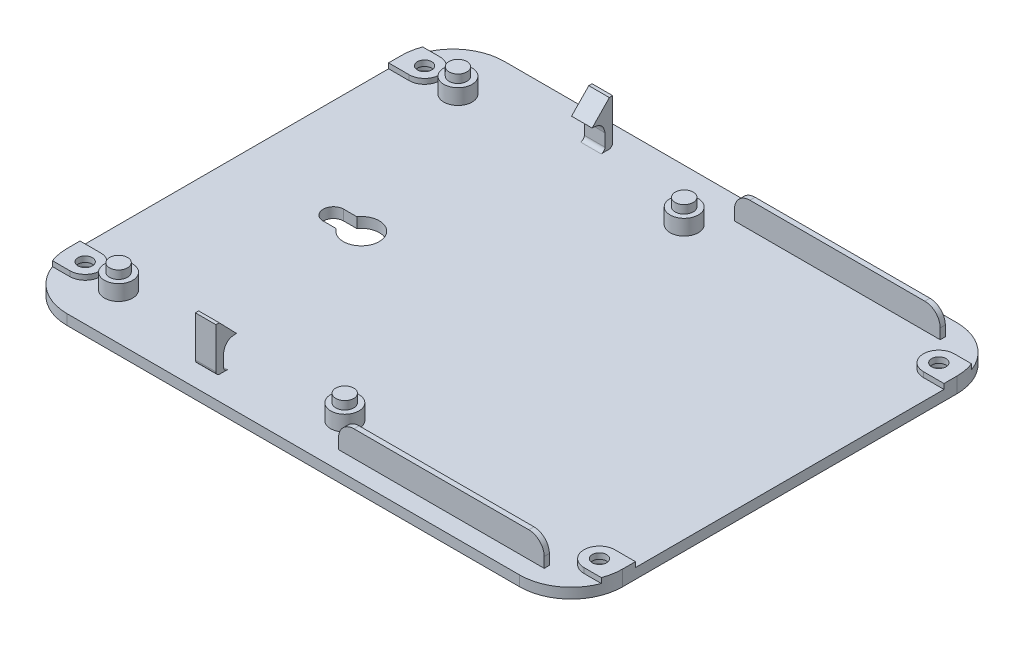
SolidWorks part; units mm, degrees
ref_plane "Front Plane" through (0, 0, 0) normal (0, 0, 1) x (1, 0, 0)
ref_plane "Top Plane" through (0, 0, 0) normal (0, 1, 0) x (1, 0, 0)
ref_plane "Right Plane" through (0, 0, 0) normal (1, 0, 0) x (0, 0, -1)
sketch "Sketch1" plane through (0, 0, 0) normal (0, 1, 0) x (1, 0, 0)
  line L0 (58.999, 8.4848) -> (96.6216, 8.4848) construction
  line L10 (-30.001, 50.9848) -> (57.999, 50.9848)
  line L11 (-40.001, 40.9848) -> (-40.001, -24.0152)
  line L12 (-30.001, -34.0152) -> (57.999, -34.0152)
  line L13 (67.999, 40.9848) -> (67.999, -24.0152)
  line L18 (-28.001, 48.9848) -> (55.999, 48.9848)
  line L19 (-38.001, 38.9848) -> (-38.001, -22.0152)
  line L20 (-28.001, -32.0152) -> (55.999, -32.0152)
  line L21 (65.999, 38.9848) -> (65.999, -22.0152)
  arc A12 (-40.001, 40.9848) -> (-30.001, 50.9848) centre (-30.001, 40.9848) cw
  arc A13 (-28.001, 48.9848) -> (-38.001, 38.9848) centre (-28.001, 38.9848) ccw
  arc A14 (67.999, -24.0152) -> (57.999, -34.0152) centre (57.999, -24.0152) cw
  arc A15 (65.999, -22.0152) -> (55.999, -32.0152) centre (55.999, -22.0152) cw
  arc A16 (67.999, 40.9848) -> (57.999, 50.9848) centre (57.999, 40.9848) ccw
  arc A17 (65.999, 38.9848) -> (55.999, 48.9848) centre (55.999, 38.9848) ccw
  arc A18 (-40.001, -24.0152) -> (-30.001, -34.0152) centre (-30.001, -24.0152) ccw
  arc A19 (-38.001, -22.0152) -> (-28.001, -32.0152) centre (-28.001, -22.0152) ccw
  point P0 (0, 0)
  point P6 (0, 0)
  point P29 (-28.001, 45.2348)
  point P31 (-28.001, 45.2348)
  point P35 (15.999, 45.2348)
  point P41 (15.999, -28.2652)
  point P47 (-28.001, -28.2652)
  dimension "D21" = 10
  dimension "D22" = 10
  dimension "D8" = 42.5
  dimension "D9" = 42.5
  dimension "D16" = 2
  dimension "D17" = 2
  dimension "D18" = 2
  dimension "D19" = 2
sketch "Sketch3" plane through (0, 0, 0) normal (0, 1, 0) x (1, 0, 0)
  line L0 (-30.001, -34.0152) -> (57.999, -34.0152) construction
  line L1 (67.999, 40.9848) -> (67.999, -24.0152) construction
  line L2 (-30.001, 50.9848) -> (57.999, 50.9848) construction
  line L3 (-40.001, 40.9848) -> (-40.001, -24.0152) construction
  line L4 (-30.001, -34.0152) -> (57.999, -34.0152)
  line L5 (67.999, 40.9848) -> (67.999, -24.0152)
  line L6 (-30.001, 50.9848) -> (57.999, 50.9848)
  line L7 (-40.001, 40.9848) -> (-40.001, -24.0152)
  arc A0 (-40.001, -24.0152) -> (-30.001, -34.0152) centre (-30.001, -24.0152) ccw construction
  arc A1 (57.999, -34.0152) -> (67.999, -24.0152) centre (57.999, -24.0152) ccw construction
  arc A2 (67.999, 40.9848) -> (57.999, 50.9848) centre (57.999, 40.9848) ccw construction
  arc A3 (-30.001, 50.9848) -> (-40.001, 40.9848) centre (-30.001, 40.9848) ccw construction
  arc A4 (-40.001, -24.0152) -> (-30.001, -34.0152) centre (-30.001, -24.0152) ccw
  arc A5 (57.999, -34.0152) -> (67.999, -24.0152) centre (57.999, -24.0152) ccw
  arc A6 (67.999, 40.9848) -> (57.999, 50.9848) centre (57.999, 40.9848) ccw
  arc A7 (-30.001, 50.9848) -> (-40.001, 40.9848) centre (-30.001, 40.9848) ccw
  dimension "D1" = 88
  dimension "D2" = 65
extrude "Boss-Extrude2" add sketch "Sketch3" along normal blind 2
sketch "Sketch5" plane through (0, 0, 34.0152) normal (0, 1, 0) x (1, 0, 0)
  line L0 (13.999, 83) -> (13.999, 110.4401) construction
  line L1 (-36.001, 78.5) -> (-39.3685, 78.5)
  line L2 (-36.001, 72.5) -> (-40.001, 72.5)
  line L3 (-40.001, 75) -> (-40.001, 10) construction
  line L4 (63.999, 78.5) -> (67.3665, 78.5)
  line L5 (63.999, 72.5) -> (67.999, 72.5)
  line L8 (63.999, 12.5) -> (67.999, 12.5)
  line L9 (67.999, 10) -> (67.999, 75) construction
  line L10 (63.999, 6.5) -> (67.3665, 6.5)
  line L11 (-36.001, 12.5) -> (-40.001, 12.5)
  line L12 (-36.001, 6.5) -> (-39.3685, 6.5)
  line L13 (67.999, 10) -> (67.999, 12.5)
  line L14 (-40.001, 75) -> (-40.001, 72.5)
  line L15 (67.999, 72.5) -> (67.999, 75)
  line L16 (-40.001, 12.5) -> (-40.001, 10)
  arc A0 (-30.001, 85) -> (-40.001, 75) centre (-30.001, 75) ccw construction
  arc A1 (67.999, 75) -> (57.999, 85) centre (57.999, 75) ccw construction
  arc A2 (57.999, 0) -> (67.999, 10) centre (57.999, 10) ccw construction
  arc A4 (-36.001, 6.5) -> (-36.001, 12.5) centre (-36.001, 9.5) ccw
  arc A5 (63.999, 12.5) -> (63.999, 6.5) centre (63.999, 9.5) ccw
  arc A6 (63.999, 78.5) -> (63.999, 72.5) centre (63.999, 75.5) ccw
  arc A7 (-36.001, 72.5) -> (-36.001, 78.5) centre (-36.001, 75.5) ccw
  arc A9 (-40.001, 10) -> (-30.001, 0) centre (-30.001, 10) ccw construction
  arc A10 (67.999, 75) -> (67.3665, 78.5) centre (57.999, 75) ccw
  arc A11 (67.3665, 6.5) -> (67.999, 10) centre (57.999, 10) ccw
  arc A12 (-40.001, 10) -> (-39.3685, 6.5) centre (-30.001, 10) ccw
  arc A13 (-39.3685, 78.5) -> (-40.001, 75) centre (-30.001, 75) ccw
  dimension "D1" = 6
  dimension "D2" = 6
  dimension "D3" = 6
  dimension "D4" = 6
  dimension "D5" = 50
  dimension "D6" = 50
  dimension "D7" = 50
  dimension "D8" = 50
sketch "Sketch6" plane through (0, 2, 0) normal (0, 1, 0) x (1, 0, 0)
  line L0 (-40.001, 8.4848) -> (67.999, 8.4848) construction
  line L1 (-40.001, 40.9848) -> (-40.001, -24.0152) construction
  line L2 (67.999, -24.0152) -> (67.999, 40.9848) construction
  line L3 (-15.3091, 50.9848) -> (-15.3091, -34.0152) construction
  line L4 (57.999, 50.9848) -> (-30.001, 50.9848) construction
  line L5 (-30.001, -34.0152) -> (57.999, -34.0152) construction
  line L6 (-16.9035, 8.4848) -> (-16.9035, 10.4848) construction
  line L8 (-16.9035, 8.4848) -> (-16.9035, 6.4848) construction
  line L9 (-16.9035, 8.4848) -> (-20.7218, 8.4848) construction
  line L10 (-18.1821, 6.4858) -> (-20.7218, 6.4858)
  line L11 (-18.1821, 10.4838) -> (-20.7218, 10.4838)
  arc A0 (-18.1821, 6.4858) -> (-18.1821, 10.4838) centre (-15.3091, 8.4848) ccw
  arc A2 (-20.7218, 10.4838) -> (-20.7218, 6.4858) centre (-20.7218, 8.4848) ccw
  point P16 (-18.8126, 8.4848)
  dimension "D1" = 7
  dimension "D2" = 2
  dimension "D3" = 2
  dimension "D4" = 1.5944
extrude "Cut-Extrude2" cut sketch "Sketch6" against normal blind 7 contours L11 A2 L10 A0
sketch "Sketch10" plane through (0, 0, 0) normal (0, 1, 0) x (1, 0, 0)
  line L0 (19.2632, 46.4848) -> (59.2632, 46.4848)
  line L1 (59.2632, 46.4848) -> (59.2632, 47.4848)
  line L2 (59.2632, 47.4848) -> (19.2632, 47.4848)
  line L3 (19.2632, 47.4848) -> (19.2632, 46.4848)
  line L4 (19.2632, -29.5152) -> (59.2632, -29.5152)
  line L5 (59.2632, -29.5152) -> (59.2632, -30.5152)
  line L6 (59.2632, -30.5152) -> (19.2632, -30.5152)
  line L7 (19.2632, -30.5152) -> (19.2632, -29.5152)
  line L8 (60.2632, 8.4848) -> (81.8858, 8.4848) construction
  dimension "D1" = 1
  dimension "D2" = 1
  dimension "D3" = 38
  dimension "D4" = 38
extrude "Boss-Extrude3" add sketch "Sketch10" along normal blind 7
sketch "Sketch12" plane through (0, 0, 30.5152) normal (0, 0, 1) x (1, 0, 0)
  line L0 (56.2632, 7) -> (59.2632, 7)
  line L1 (59.2632, 7) -> (59.2632, 2) construction
  line L2 (19.2632, 7) -> (59.2632, 7) construction
  line L3 (59.2632, 7) -> (59.2632, 4)
  line L4 (19.2632, 4) -> (19.2632, 7)
  line L5 (19.2632, 7) -> (19.2632, 2) construction
  line L6 (19.2632, 7) -> (22.2632, 7)
  arc A0 (59.2632, 4) -> (56.2632, 7) centre (56.2632, 4) ccw
  arc A1 (19.2632, 4) -> (22.2632, 7) centre (22.2632, 4) cw
  dimension "D2" = 3
extrude "Cut-Extrude4" cut sketch "Sketch12" against normal up to surface (1 mm away) up to face at (39.2632, 4.5, 29.5152)
sketch "Sketch13" plane through (0, 0, -47.4848) normal (0, 0, -1) x (-1, 0, 0)
  line L0 (-56.2632, 7) -> (-59.2632, 7)
  line L1 (-59.2632, 7) -> (-19.2632, 7) construction
  line L2 (-59.2632, 7) -> (-59.2632, 4)
  line L3 (-19.2632, 4) -> (-19.2632, 7)
  line L4 (-19.2632, 7) -> (-19.2632, 2) construction
  line L5 (-19.2632, 7) -> (-22.2632, 7)
  arc A0 (-19.2632, 4) -> (-22.2632, 7) centre (-22.2632, 4) ccw construction
  arc A1 (-56.2632, 7) -> (-59.2632, 4) centre (-56.2632, 4) ccw construction
  arc A2 (-19.2632, 4) -> (-22.2632, 7) centre (-22.2632, 4) ccw
  arc A3 (-56.2632, 7) -> (-59.2632, 4) centre (-56.2632, 4) ccw
extrude "Cut-Extrude5" cut sketch "Sketch13" against normal up to surface (1 mm away) up to face at (39.2632, 4.5, -46.4848)
sketch "Sketch14" plane through (0, 0, 0) normal (0, -1, 0) x (1, 0, 0)
  circle A0 centre (-29.011, 25.0118) radius 1.75
  circle A1 centre (14.9819, 25.0118) radius 1.75
  circle A2 centre (14.9819, -40.9882) radius 1.75
  circle A3 centre (-29.011, -40.9882) radius 1.75
  dimension "D1" = 3.5
extrude "Boss-Extrude4" add sketch "Sketch14" against normal up to surface (6.6 mm away) contours A0 | A1 | A2 | A3
sketch "Sketch15" plane through (0, 0, 0) normal (0, -1, 0) x (1, 0, 0)
  circle A0 centre (-29.011, 25.0118) radius 2.75
  circle A1 centre (14.9819, 25.0118) radius 2.75
  circle A2 centre (14.9819, -40.9882) radius 2.75
  circle A3 centre (-29.011, -40.9882) radius 2.75
  dimension "D1" = 5.5
extrude "Boss-Extrude5" add sketch "Sketch15" against normal up to surface (5 mm away)
ref_plane "Plane1" through (-7, 0, 0) normal (1, 0, 0) x (0, 0, -1)
sketch "Sketch19" plane through (-7, 0, 0) normal (1, 0, 0) x (0, 0, -1)
  line L4 (-30.0919, 10.6908) -> (-30.0919, 2.75)
  line L5 (-29.8901, 0) -> (-28.5919, 0)
  line L6 (-28.5919, 2.75) -> (-28.5919, 5.1849)
  line L7 (-26.0931, 7.2293) -> (-29.4468, 10.6908)
  line L8 (-29.4468, 10.6908) -> (-30.0919, 10.6908)
  line L9 (8.4848, 5) -> (8.4848, 23.7297) construction
  line L12 (-27.8419, 2) -> (-27.8419, 0)
  line L13 (-27.8419, 0) -> (-29.3419, 0)
  line L14 (-29.3419, 0) -> (-29.3419, 2)
  line L15 (45.5615, 2.75) -> (45.5615, 5.1849)
  line L16 (43.0627, 7.2293) -> (46.4164, 10.6908)
  line L17 (46.4164, 10.6908) -> (47.0615, 10.6908)
  line L18 (47.0615, 10.6908) -> (47.0615, 2.75)
  line L19 (46.3115, 0) -> (46.3115, 2)
  line L20 (44.8115, 0) -> (46.3115, 0)
  line L21 (44.8115, 2) -> (44.8115, 0)
  arc A0 (-29.3419, 2) -> (-30.0919, 2.75) centre (-29.3419, 2.75) cw
  arc A1 (-27.8419, 2) -> (-28.5919, 2.75) centre (-27.8419, 2.75) cw
  arc A2 (44.8115, 2) -> (45.5615, 2.75) centre (44.8115, 2.75) ccw
  arc A3 (46.3115, 2) -> (47.0615, 2.75) centre (46.3115, 2.75) ccw
  spline S0 degree 2 poles (-28.5919, 5.1849) (-28.2832, 7.2798) (-26.0931, 7.2293) knots 0 0 0 1 1 1
  spline S1 degree 2 poles (45.5615, 5.1849) (45.2528, 7.2798) (43.0627, 7.2293) knots 0 0 0 1 1 1
  dimension "D2" = 0.75
  dimension "D3" = 0.75
  dimension "D1" = 1.5
extrude "Boss-Extrude7" add sketch "Sketch19" along normal blind 2 and the other way blind 2 contours S1 L15 A2 L21 L20 L19 A3 L18 L17 L16 | L6 S0 L7 L8 L4 A0 L14 L5 L13 L12 A1
extrude "Boss-Extrude8" add sketch "Sketch5" along normal blind 3
sketch "Sketch21" plane through (0, 0, 0) normal (0, -1, 0) x (1, 0, 0)
  circle A0 centre (-36.001, 24.5152) radius 3
  circle A1 centre (63.999, 24.5152) radius 3
  circle A2 centre (63.999, -41.4848) radius 3
  circle A3 centre (-36.001, -41.4848) radius 3
extrude "Cut-Extrude7" cut sketch "Sketch21" against normal blind 1.9
sketch "Sketch22" plane through (0, 1.9, 0) normal (0, -1, 0) x (1, 0, 0)
  circle A0 centre (-36.001, 24.5152) radius 1.4
  circle A1 centre (63.999, 24.5152) radius 1.4
  circle A2 centre (63.999, -41.4848) radius 1.4
  circle A3 centre (-36.001, -41.4848) radius 1.4
  dimension "D1" = 2.8
extrude "Cut-Extrude8" cut sketch "Sketch22" against normal blind 15
